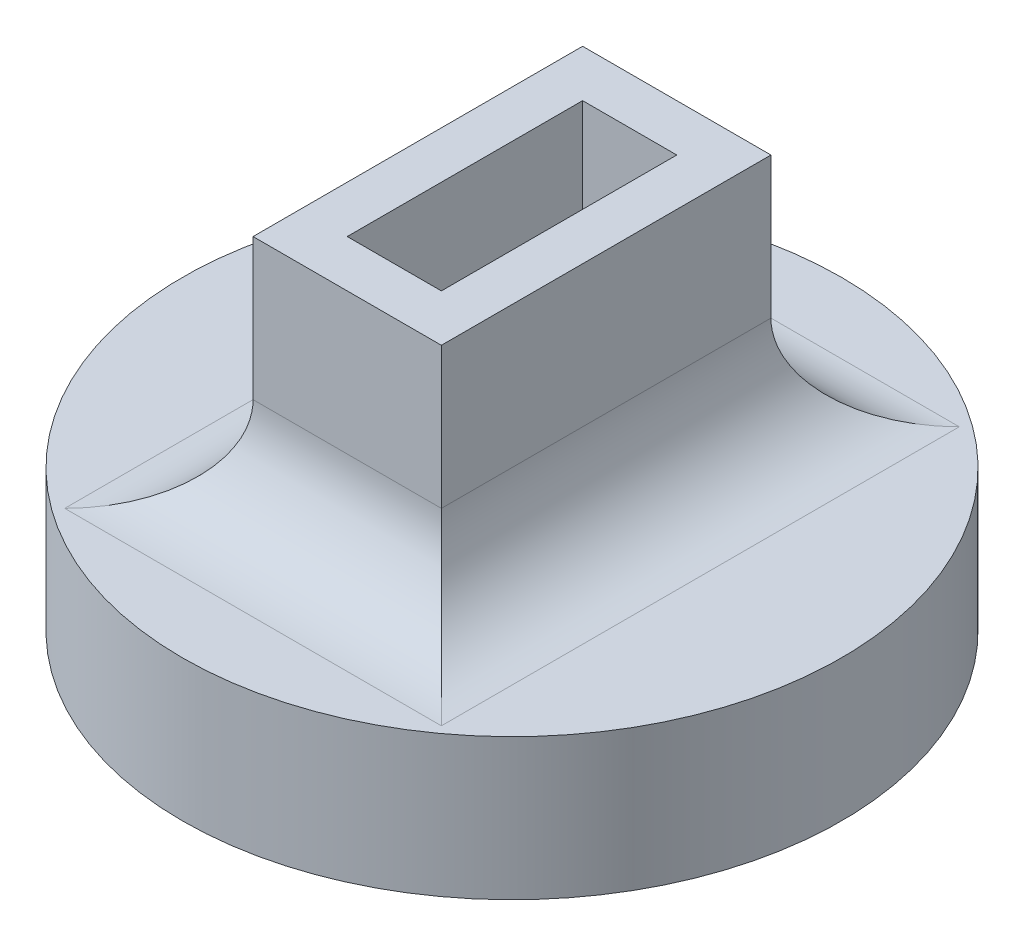
SolidWorks part; units mm, degrees
ref_plane "Front Plane" through (0, 0, 0) normal (0, 0, 1) x (1, 0, 0)
ref_plane "Top Plane" through (0, 0, 0) normal (0, 1, 0) x (1, 0, 0)
ref_plane "Right Plane" through (0, 0, 0) normal (1, 0, 0) x (0, 0, -1)
sketch "Sketch1" plane through (0, 0, 0) normal (0, 1, 0) x (1, 0, 0)
  circle A0 centre (0, 0) radius 7
  dimension "D1" = 14
extrude "Boss-Extrude1" add sketch "Sketch1" along normal blind 3
sketch "Sketch2" plane through (0, 3, 0) normal (0, 1, 0) x (1, 0, 0)
  line L1 (-1, 2.5) -> (1, 2.5)
  line L2 (-1, 2.5) -> (-1, -2.5)
  line L3 (-1, -2.5) -> (1, -2.5)
  line L4 (1, 2.5) -> (1, -2.5)
  line L5 (-1, 2.5) -> (1, -2.5) construction
  line L6 (-1, -2.5) -> (1, 2.5) construction
  line L7 (-2, 3.5) -> (2, 3.5)
  line L8 (-2, 3.5) -> (-2, -3.5)
  line L9 (-2, -3.5) -> (2, -3.5)
  line L10 (2, 3.5) -> (2, -3.5)
  line L11 (-1, 1.75) -> (1, -1.75) construction
  line L12 (-1, -1.75) -> (0.5087, 0.8903) construction
  point P0 (0, 0)
  point P6 (0, 0)
  dimension "D1" = 2
  dimension "D2" = 5
  dimension "D3" = 4
  dimension "D4" = 7
extrude "Boss-Extrude2" add sketch "Sketch2" along normal blind 5 contours L4 L1 L2 L3 | L8 L7 L10 L9
fillet "Fillet1" radius 2 4 edges at (0, 3, -3.5) (2, 3, 0) (0, 3, 3.5) (-2, 3, 0)
